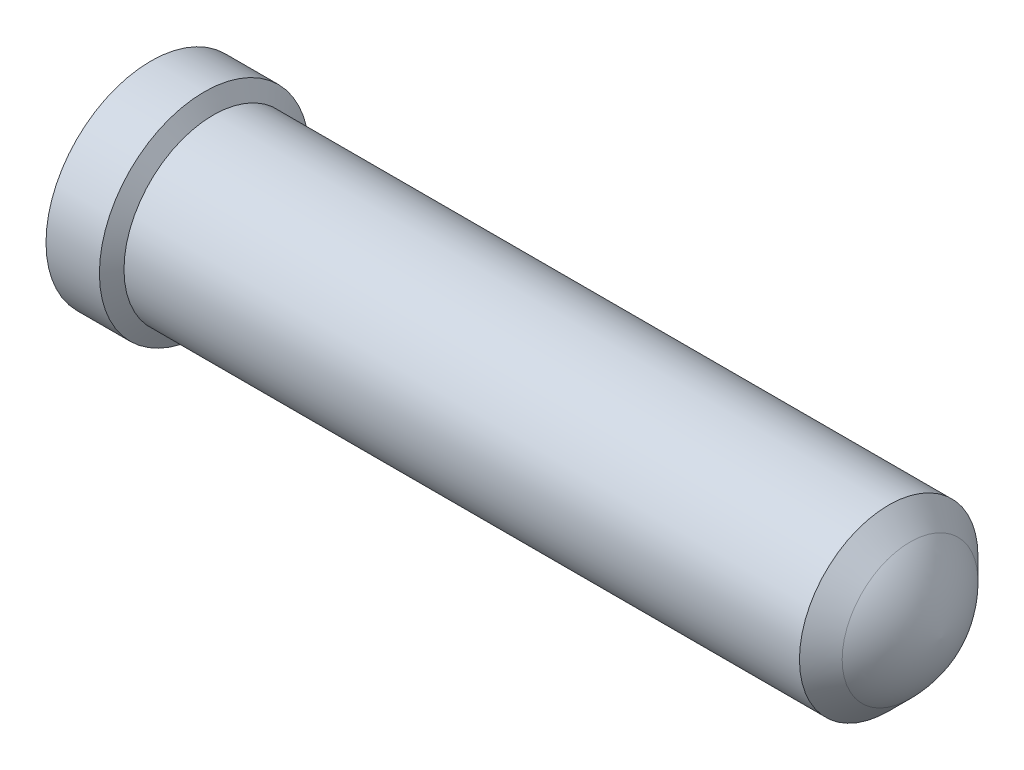
SolidWorks part; units mm, degrees
material "Brass Alloy 385"
ref_plane "Front Plane" through (0, 0, 0) normal (0, 0, 1) x (1, 0, 0)
ref_plane "Top Plane" through (0, 0, 0) normal (0, 1, 0) x (1, 0, 0)
ref_plane "Right Plane" through (0, 0, 0) normal (1, 0, 0) x (0, 0, -1)
sketch "Sketch1" plane through (0, 0, 0) normal (0, 0, 1) x (1, 0, 0)
  line L0 (0, 0) -> (0, 0.6236)
  line L1 (0, 0.6236) -> (0.3175, 0.6236)
  line L2 (0.3175, 0.6236) -> (0.371, 0.5309)
  line L3 (0.371, 0.5309) -> (4.3876, 0.5309)
  line L4 (4.3876, 0.5309) -> (4.5146, 0.4039)
  line L5 (0, 0) -> (4.699, 0)
  line L6 (0, 0) -> (4.699, 0) construction
  arc A0 (4.699, 0) -> (4.5146, 0.4039) centre (4.0656, -0.0452) ccw
revolve "RevolutionAngle1" add sketch "Sketch1" angle 360 about L6
hole_wizard "Hole1" positions "Sketch3" profile "Sketch2" legacy
sketch "Sketch3" plane through (0, 0, 0) normal (-1, 0, 0) x (0, 0, 1)
  point P0 (0, 0)
sketch "Sketch2" plane through (0, 0, 0) normal (0, 1, 0) x (0, 0, 1)
  line L0 (0, 0) -> (0, 2.8147)
  line L1 (0, 2.8147) -> (0.4572, 2.54)
  line L2 (0.4572, 2.54) -> (0.4572, 0.0889)
  line L3 (0.4572, 0.0889) -> (0.5461, 0)
  line L4 (0.5461, 0) -> (0, 0)
  line L5 (0, -14.3089) -> (0, 102.4216) construction
  line L6 (0, 2.8147) -> (-0.4572, 2.54) construction
  line L7 (-0.4572, 0.0889) -> (-0.5461, 0) construction
  dimension "Diameter" = 0.9144
  dimension "Depth" = 2.54
  dimension "C-Sink Diameter" = 1.0922
  dimension "C-Sink Angle" = 90
  dimension "Drill Angle" = 118
